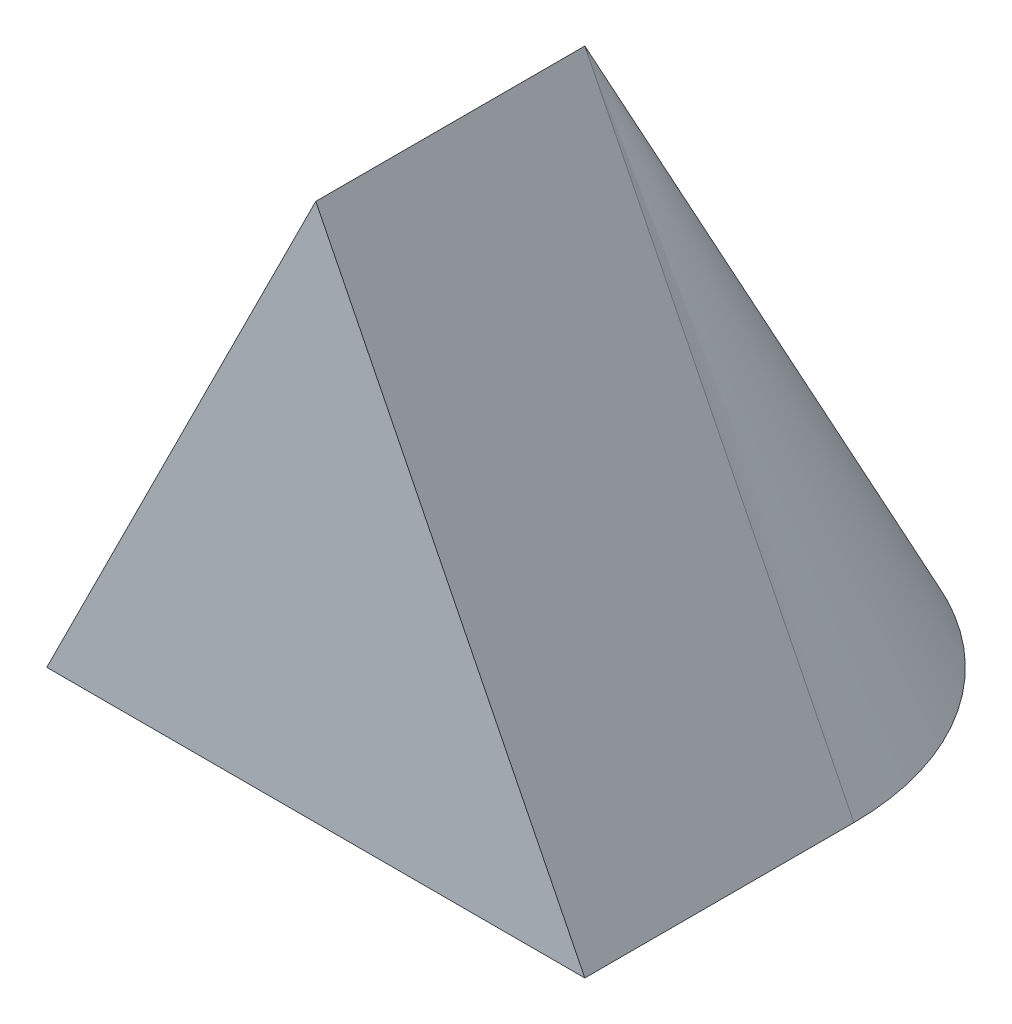
SolidWorks part; units mm, degrees
material "Polyurethane Foam Rigid"
ref_plane "Front Plane" through (0, 0, 0) normal (0, 0, 1) x (1, 0, 0)
ref_plane "Top Plane" through (0, 0, 0) normal (0, 1, 0) x (1, 0, 0)
ref_plane "Right Plane" through (0, 0, 0) normal (1, 0, 0) x (0, 0, -1)
sketch "Sketch1" plane through (0, 0, 0) normal (0, 0, 1) x (1, 0, 0)
  line L0 (0, 110.0667) -> (0, -125.9417) construction
  line L1 (0, 136.525) -> (-101.6, -66.675)
  line L2 (-101.6, -66.675) -> (0, -66.675)
  line L3 (0, 136.525) -> (0, -66.675)
  dimension "D1" = 101.6
  dimension "D2" = 203.2
revolve "Revolve1" add sketch "Sketch1" angle 180 about L0
sketch "Sketch2" plane through (0, 0, 0) normal (0, 0, 1) x (1, 0, 0)
  line L0 (0, 136.525) -> (-101.6, -66.675)
  line L1 (-101.6, -66.675) -> (101.6, -66.675)
  line L2 (101.6, -66.675) -> (0, 136.525)
extrude "Boss-Extrude1" add sketch "Sketch2" along normal blind 101.6
sketch "Sketch3" plane through (-54.61, 27.305, 0) normal (-0.8944, 0.4472, 0) x (0, 0, 1)
  line L1 (101.6, 122.1117) -> (101.6, -105.0728) construction
  line L2 (101.6, -105.0728) -> (0, -105.0728) construction
  line L3 (101.6, -105.0728) -> (101.6, 122.1117)
